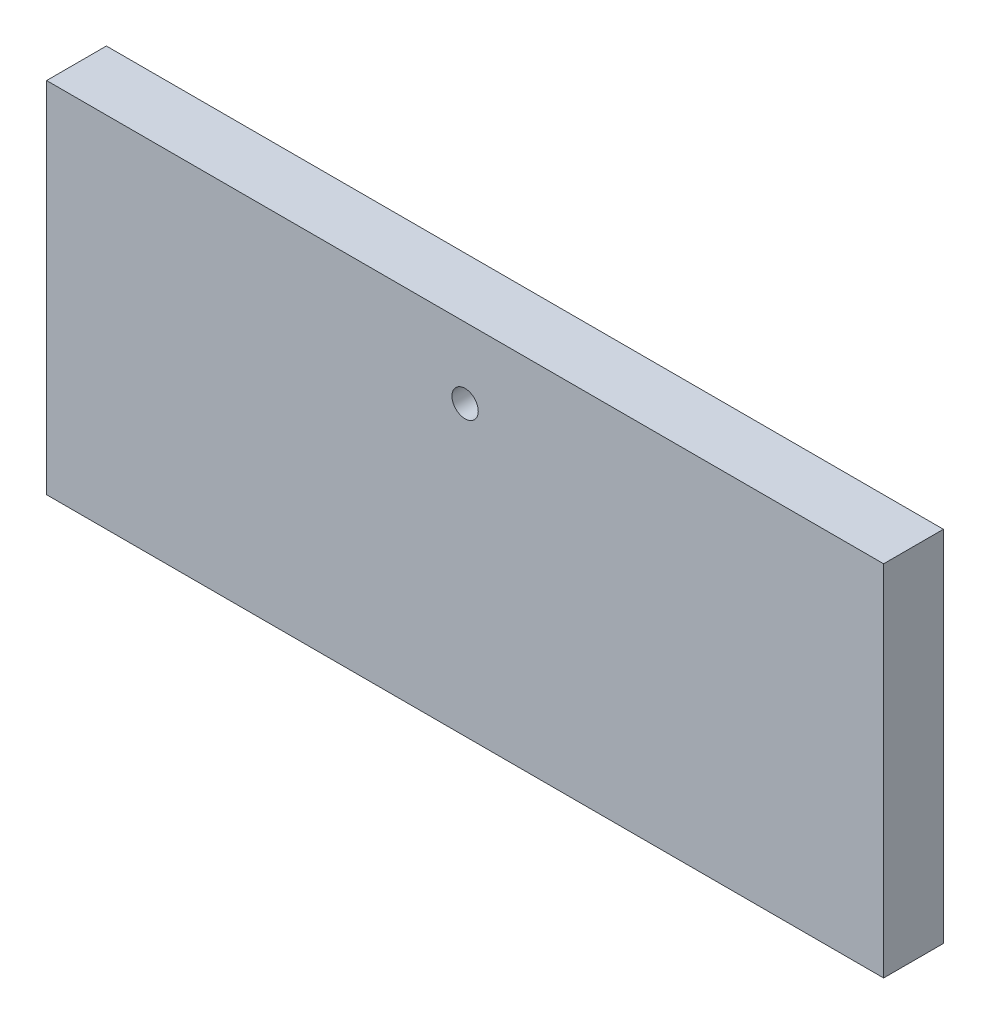
SolidWorks part; units mm, degrees
material "Plain Carbon Steel"
ref_plane "Front Plane" through (0, 0, 0) normal (0, 0, 1) x (1, 0, 0)
ref_plane "Top Plane" through (0, 0, 0) normal (0, 1, 0) x (1, 0, 0)
ref_plane "Right Plane" through (0, 0, 0) normal (1, 0, 0) x (0, 0, -1)
sketch "Sketch1" plane through (0, 0, 0) normal (0, 0, 1) x (1, 0, 0)
  line L0 (-350, 0) -> (350, 0)
  line L1 (-350, 0) -> (-350, 300)
  line L2 (350, 0) -> (350, 300)
  line L3 (-350, 300) -> (350, 300)
  line L4 (-350, 0) -> (350, 300) construction
  line L5 (350, 0) -> (-350, 300) construction
  line L6 (0, 0) -> (0, 101.3058) construction
  point P1 (0, 150)
  dimension "D1" = 700
  dimension "D2" = 300
extrude "Boss-Extrude1" add sketch "Sketch1" along normal mid plane 50
sketch "Sketch2" plane through (0, 0, 0) normal (0, 0, 1) x (1, 0, 0)
  line L0 (0, 0) -> (0, 300.3172) construction
  line L1 (350, 300) -> (-350, 300) construction
  circle A0 centre (0, 241) radius 11
  dimension "D2" = 22
  dimension "D1" = 59
extrude "Cut-Extrude1" cut sketch "Sketch2" along normal through all and the other way through all
